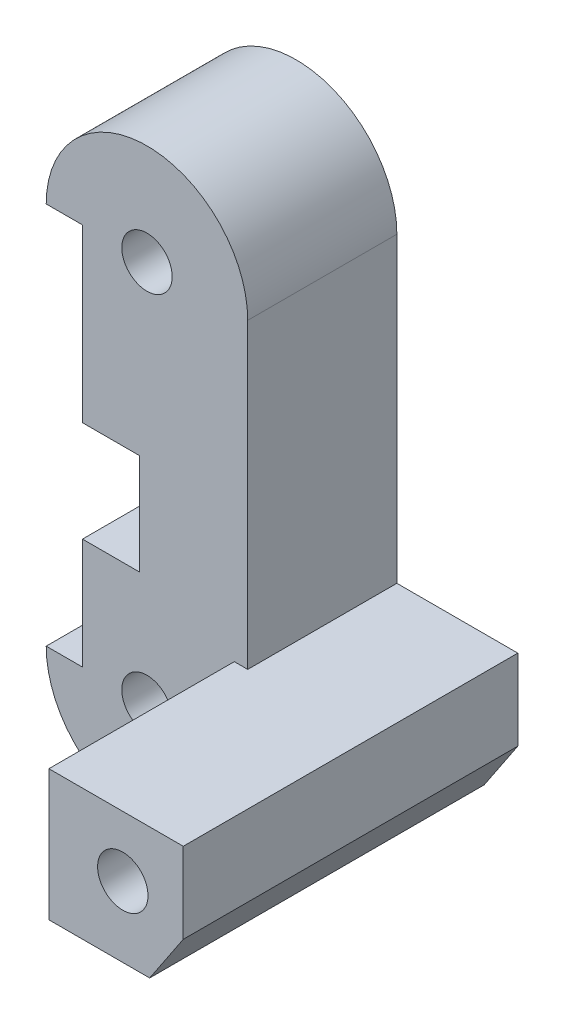
SolidWorks part; units mm, degrees
ref_plane "前视基准面" through (0, 0, 0) normal (0, 0, 1) x (1, 0, 0)
ref_plane "上视基准面" through (0, 0, 0) normal (0, 1, 0) x (1, 0, 0)
ref_plane "右视基准面" through (0, 0, 0) normal (1, 0, 0) x (0, 0, -1)
sketch "草图1" plane through (0, 0, 0) normal (0, 0, 1) x (1, 0, 0)
  line L0 (-3.2, 19) -> (-3.2, 0)
  line L1 (-3.2, 0) -> (-5, 0)
  line L2 (4.3333, -2.4944) -> (9.3333, -2.4944)
  line L3 (9.3333, -2.4944) -> (11, 0)
  line L4 (11, 0) -> (11, 4)
  line L5 (11, 4) -> (5, 4)
  line L6 (5, 4) -> (5, 19)
  line L7 (-3.2, 19) -> (-5, 19)
  line L8 (0, 24) -> (11, 24) construction
  arc A0 (-5, 0) -> (4.3333, -2.4944) centre (0, 0) ccw
  arc A1 (5, 19) -> (-5, 19) centre (0, 19) ccw
  dimension "D1" = 5
  dimension "D4" = 5
  dimension "D2" = 1.8
  dimension "D3" = 19
  dimension "D5" = 5
  dimension "D6" = 3
  dimension "D7" = 4
  dimension "D8" = 6
  dimension "D9" = 15
extrude "凸台-拉伸1" add sketch "草图1" along normal blind 7.4
sketch "草图2" plane through (0, 0, 7.4) normal (0, 0, 1) x (1, 0, 0)
  line L0 (11, 4) -> (5, 4) construction
  line L1 (11, 0) -> (11, 4) construction
  line L2 (9.3333, -2.4944) -> (11, 0) construction
  line L3 (4.3333, -2.4944) -> (9.3333, -2.4944) construction
  line L4 (11, 4) -> (5, 4)
  line L5 (11, 0) -> (11, 4)
  line L6 (9.3333, -2.4944) -> (11, 0)
  line L7 (4.3333, -2.4944) -> (9.3333, -2.4944)
  line L8 (4.3333, -2.4944) -> (4.3333, 4)
  line L9 (5, 4) -> (4.3333, 4)
extrude "凸台-拉伸2" add sketch "草图2" along normal blind 9.2
sketch "草图3" plane through (0, 0, 7.4) normal (0, 0, 1) x (1, 0, 0)
  line L0 (0, 0) -> (0, 23.2652) construction
  circle A0 centre (0, 0) radius 1.5 construction
  circle A1 centre (0, 19) radius 1.5 construction
  dimension "D1" = 3
  dimension "D2" = 3
sketch "草图4" plane through (0, 0, 16.6) normal (0, 0, 1) x (1, 0, 0)
  line L0 (11, 4) -> (4.3333, 4) construction
  circle A0 centre (8, 1) radius 1.5 construction
  dimension "D3" = 3
  dimension "D1" = 8
  dimension "D2" = 3
sketch "草图5" plane through (-3.2, 0, 0) normal (-1, 0, 0) x (0, 0, 1)
  line L0 (4.4, 20) -> (4.4, 0) construction
  line L2 (7.4, 0) -> (0, 0) construction
  line L3 (7.4, 19) -> (7.4, 0) construction
  circle A0 centre (4.4, 4) radius 1.5 construction
  circle A1 centre (4.4, 14) radius 1.5 construction
  dimension "D1" = 3
  dimension "D2" = 4
  dimension "D3" = 10
  dimension "D4" = 3
hole_wizard "M3 螺纹孔1" positions "3D草图1" profile "草图6" tap size "M3" standard "GB"
sketch3d "3D草图1"
  point P0 (-3.2, 14, 4.4)
  point P3 (-3.2, 4, 4.4)
sketch "草图6" plane through (-3.2, 14, 4.4) normal (0, 1, 0) x (0, 0, 1)
  line L0 (0, 0) -> (0, 7.2511)
  line L1 (0, 7.2511) -> (1.25, 6.5)
  line L2 (1.25, 6.5) -> (1.25, 0)
  line L5 (1.25, 0) -> (0, 0)
  line L10 (0, 7.2511) -> (-1.25, 6.5) construction
  line L11 (0, -6.35) -> (0, 107.95) construction
  dimension "螺纹孔钻头直径" = 2.5
  dimension "螺纹孔钻头深度" = 6.5
  dimension "导头角度" = 118
cosmetic thread "孔螺蚊线1" parameters "D1"=4, "D2"=3
cosmetic thread "孔螺蚊线2" parameters "D1"=4, "D2"=3
hole_wizard "M3 螺纹孔3" positions "3D草图3" profile "草图8" tap size "M3" standard "GB" end condition through all
sketch3d "3D草图3"
  point P0 (0, 0, 7.4)
  point P3 (0, 19, 7.4)
sketch "草图8" plane through (0, 0, 7.4) normal (1, 0, 0) x (0, -1, 0)
  line L0 (0, 0) -> (0, 7.4)
  line L1 (0, 7.4) -> (1.25, 7.4)
  line L2 (1.25, 7.4) -> (1.25, 0)
  line L5 (1.25, 0) -> (0, 0)
  line L11 (0, -6.35) -> (0, 107.95) construction
  dimension "通孔螺纹孔钻头直径" = 2.5
  dimension "通孔螺纹孔钻头深度" = 7.4
cosmetic thread "孔螺蚊线3" parameters "D2"=3
cosmetic thread "孔螺蚊线4" parameters "D2"=3
hole_wizard "M3 螺纹孔4" positions "3D草图4" profile "草图9" tap size "M3" standard "GB" end condition through all
sketch3d "3D草图4"
  point P0 (8, 1, 16.6)
sketch "草图9" plane through (8, 1, 16.6) normal (1, 0, 0) x (0, -1, 0)
  line L0 (0, 0) -> (0, 16.6)
  line L1 (0, 16.6) -> (1.25, 16.6)
  line L2 (1.25, 16.6) -> (1.25, 0)
  line L5 (1.25, 0) -> (0, 0)
  line L11 (0, -6.35) -> (0, 107.95) construction
  dimension "通孔螺纹孔钻头直径" = 2.5
  dimension "通孔螺纹孔钻头深度" = 16.6
cosmetic thread "孔螺蚊线5" parameters "D2"=3
fillet "圆角1" radius 2 1 edges at (4.3333, -2.4944, 3.7)
ref_plane "基准面1" through (0, 5.5, 0) normal (0, 1, 0) x (1, 0, 0)
sketch "草图10" plane through (0, 5.5, 0) normal (0, 1, 0) x (1, 0, 0)
  line L0 (-3.2, -7.4) -> (-0.3716, -7.4)
  line L1 (-0.3716, -7.4) -> (-3.2, -4.5716)
  line L2 (-3.2, -4.5716) -> (-3.2, -7.4)
  line L3 (-3.2, -7.4) -> (-5, -7.4) construction
  line L4 (-3.2, -7.4) -> (-5, -7.4) construction
  line L5 (-3.2, -7.4) -> (-5, -7.4) construction
  dimension "D1" = 4
extrude "切除-拉伸1" cut sketch "草图10" along normal blind 5
